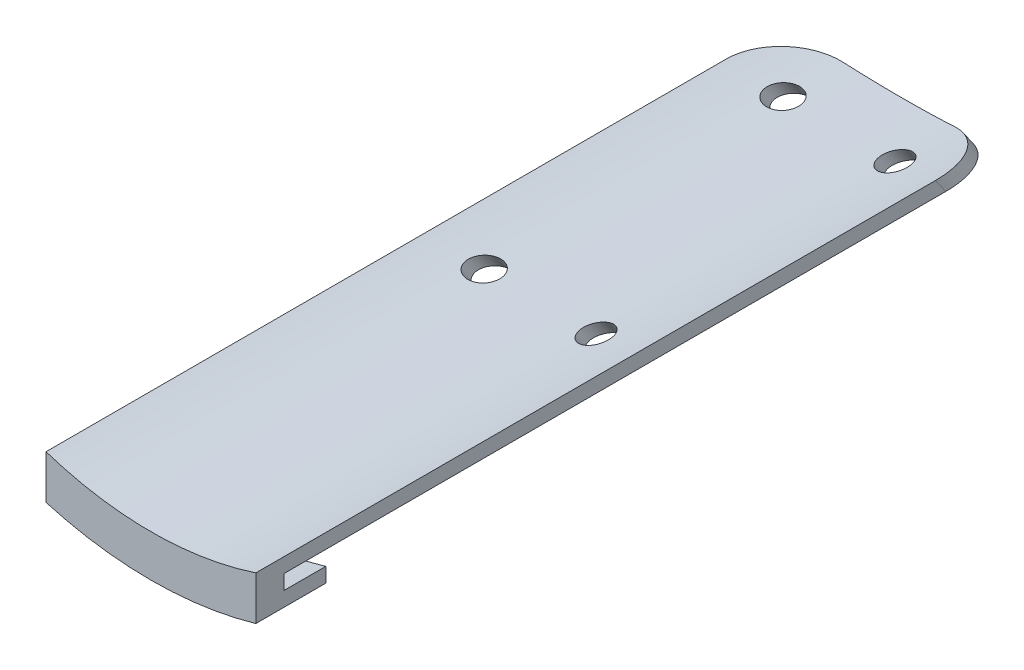
SolidWorks part; units mm, degrees
ref_plane "Front Plane" through (0, 0, 0) normal (0, 0, 1) x (1, 0, 0)
ref_plane "Top Plane" through (0, 0, 0) normal (0, 1, 0) x (1, 0, 0)
ref_plane "Right Plane" through (0, 0, 0) normal (1, 0, 0) x (0, 0, -1)
sketch "Sketch1" plane through (0, 0, 0) normal (0, 0, 1) x (1, 0, 0)
  line L0 (50, 64.2983) -> (48, 64.2983)
  line L1 (-48, 64.2983) -> (-50, 64.2983)
  arc A1 (-48, 64.2983) -> (48, 64.2983) centre (0, 64.2983) ccw
  circle A2 centre (0, 64.2983) radius 50
  arc A3 (-50, 64.2983) -> (50, 64.2983) centre (0, 64.2983) ccw
  circle A4 centre (0, 64.2983) radius 50 construction
  circle A5 centre (0, 64.2983) radius 48 construction
  dimension "D1" = 2
  dimension "D2" = 2
extrude "Boss-Extrude1" add sketch "Sketch1" along normal up to vertex (161.2082 mm away)
sketch "Sketch3" plane through (0, 0, 161.2082) normal (0, 0, 1) x (1, 0, 0)
  line L2 (50, 64.2983) -> (48, 64.2983)
  line L3 (-48, 64.2983) -> (-50, 64.2983)
  line L4 (50, 64.2983) -> (48, 64.2983)
  line L5 (-48, 64.2983) -> (-50, 64.2983)
  arc A2 (-50, 64.2983) -> (50, 64.2983) centre (0, 64.2983) ccw
  arc A3 (-48, 64.2983) -> (48, 64.2983) centre (0, 64.2983) ccw
  arc A4 (-50, 64.2983) -> (50, 64.2983) centre (0, 64.2983) ccw
  arc A5 (-48, 64.2983) -> (48, 64.2983) centre (0, 64.2983) ccw
  dimension "D1" = 0
extrude "Boss-Extrude2" add sketch "Sketch3" along normal blind 4
sketch "Sketch4" plane through (0, 0, 165.2082) normal (0, 0, 1) x (1, 0, 0)
  line L0 (-54, 64.2983) -> (-52, 64.2983)
  line L1 (52, 64.2983) -> (54, 64.2983)
  arc A1 (-54, 64.2983) -> (54, 64.2983) centre (0, 64.2983) ccw
  arc A2 (-52, 64.2983) -> (52, 64.2983) centre (0, 64.2983) ccw
  arc A3 (-52, 64.2983) -> (52, 64.2983) centre (0, 64.2983) ccw
  dimension "D1" = 2
  dimension "D2" = 2
extrude "Boss-Extrude3" add sketch "Sketch4" against normal blind 10 separate body
sketch "Sketch5" plane through (0, 0, 165.2082) normal (0, 0, 1) x (1, 0, 0)
  line L2 (-50, 64.2983) -> (-52, 64.2983)
  line L3 (52, 64.2983) -> (50, 64.2983)
  line L4 (-50, 64.2983) -> (-52, 64.2983)
  line L5 (52, 64.2983) -> (50, 64.2983)
  arc A2 (-50, 64.2983) -> (50, 64.2983) centre (0, 64.2983) ccw
  arc A3 (-52, 64.2983) -> (52, 64.2983) centre (0, 64.2983) ccw
  arc A4 (-50, 64.2983) -> (50, 64.2983) centre (0, 64.2983) ccw
  arc A5 (-52, 64.2983) -> (52, 64.2983) centre (0, 64.2983) ccw
  dimension "D1" = 0
extrude "Boss-Extrude4" add sketch "Sketch5" against normal blind 4 contours A4 L5 A5 L4
ref_plane "Plane1" through (0, 66.7881, 46.7655) normal (0, -0.8192, -0.5736) x (-1, 0, 0)
sketch "Sketch6" plane through (0, 66.7881, 46.7655) normal (0, -0.8192, -0.5736) x (-1, 0, 0)
  line L0 (0, -95) -> (0, -30) construction
  line L1 (0, -95) -> (0, -30) construction
  line L2 (-15, -128.2048) -> (-15, -45)
  line L3 (-8, -38) -> (8, -38)
  line L4 (54, -98.4506) -> (54, 36.88)
  line L7 (15, -128.2048) -> (15, -45)
  line L13 (54, 36.88) -> (-54, 36.88)
  line L15 (-54, 36.88) -> (-54, -98.4506)
  circle A0 centre (-8, -80) radius 2 construction
  circle A1 centre (8, -80) radius 2 construction
  circle A2 centre (8, -45) radius 2 construction
  circle A3 centre (-8, -45) radius 2 construction
  circle A4 centre (-8, -80) radius 2
  circle A5 centre (8, -80) radius 2
  circle A6 centre (8, -45) radius 2
  circle A7 centre (-8, -45) radius 2
  arc A8 (-15, -45) -> (-8, -38) centre (-8, -45) cw
  arc A11 (15, -45) -> (8, -38) centre (8, -45) ccw
  ellipse E0 centre (0, -98.4506) end of major axis (-54, -98.4506) minor radius 30.9731 (-54, -98.4506) -> (54, -98.4506) ccw construction
  ellipse E1 centre (0, -98.4506) end of major axis (-54, -98.4506) minor radius 30.9731 (-54, -98.4506) -> (-15, -128.2048) ccw
  ellipse E2 centre (0, -98.4506) end of major axis (-54, -98.4506) minor radius 30.9731 (15, -128.2048) -> (54, -98.4506) ccw
  point P24 (-54, 36.88)
  point P32 (54, 36.88)
  point P43 (0, -38)
  dimension "D1" = 7
extrude "Cut-Extrude1" cut sketch "Sketch6" against normal through all both and the other way through all
